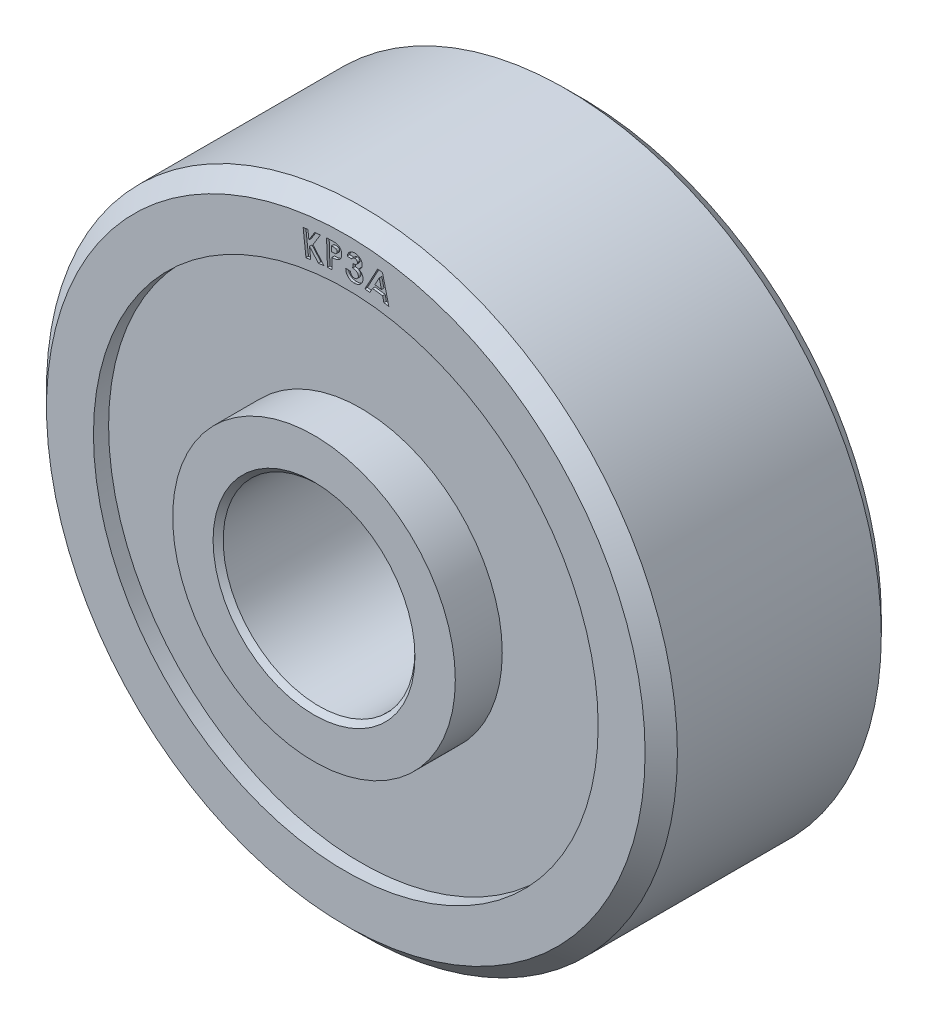
SolidWorks part; units mm, degrees
ref_plane "Front Plane" through (0, 0, 0) normal (0, 0, 1) x (1, 0, 0)
ref_plane "Top Plane" through (0, 0, 0) normal (0, 1, 0) x (1, 0, 0)
ref_plane "Right Plane" through (0, 0, 0) normal (1, 0, 0) x (0, 0, -1)
sketch "Sketch1" plane through (0, 0, 0) normal (1, 0, 0) x (0, 0, -1)
  line L0 (0, 0) -> (63.1482, 0) construction
  line L1 (-3.7719, 2.54) -> (-3.7719, 3.556)
  line L2 (-3.7719, 3.556) -> (-2.5908, 3.556)
  line L3 (-2.5908, 3.556) -> (-2.5908, 6.35)
  line L4 (-2.5908, 6.35) -> (-2.9718, 6.35)
  line L5 (-2.9718, 6.35) -> (-2.9718, 7.5311)
  line L6 (-2.9718, 7.5311) -> (-2.5654, 7.9375)
  line L7 (-2.5654, 7.9375) -> (2.5654, 7.9375)
  line L8 (-3.6449, 2.413) -> (3.6449, 2.413)
  line L9 (0, 0) -> (0, 42.8623) construction
  line L10 (2.9718, 7.5311) -> (2.5654, 7.9375)
  line L11 (2.9718, 6.35) -> (2.9718, 7.5311)
  line L12 (2.5908, 6.35) -> (2.9718, 6.35)
  line L13 (2.5908, 3.556) -> (2.5908, 6.35)
  line L14 (3.7719, 3.556) -> (2.5908, 3.556)
  line L15 (3.7719, 2.54) -> (3.7719, 3.556)
  line L16 (3.6449, 2.413) -> (3.7719, 2.54)
  line L17 (-3.7719, 2.54) -> (-3.6449, 2.413)
  point P3 (-3.7719, 2.413)
  point P19 (3.7719, 2.413)
  dimension "D1" = 4.826
  dimension "D2" = 7.112
  dimension "D3" = 7.5438
  dimension "D4" = 5.9436
  dimension "D5" = 0.381
  dimension "D6" = 12.7
  dimension "D7" = 45
  dimension "D8" = 0.4064
  dimension "D9" = 15.875
revolve "Revolve1" add sketch "Sketch1" angle 360 about L0
sketch "Sketch2" plane through (0, 0, 2.9718) normal (0, 0, 1) x (1, 0, 0)
  line L0 (0, 0) -> (0, 6.604) construction
  arc A1 (-1.0747, 6.516) -> (1.0747, 6.516) centre (0, 0) cw construction
  text T0 "KP3A" font "Century Gothic" height 0.635
  dimension "D1" = 6.604
  dimension "D2" = 2.159
extrude "Cut-Extrude1" cut sketch "Sketch2" against normal blind 0.0635
